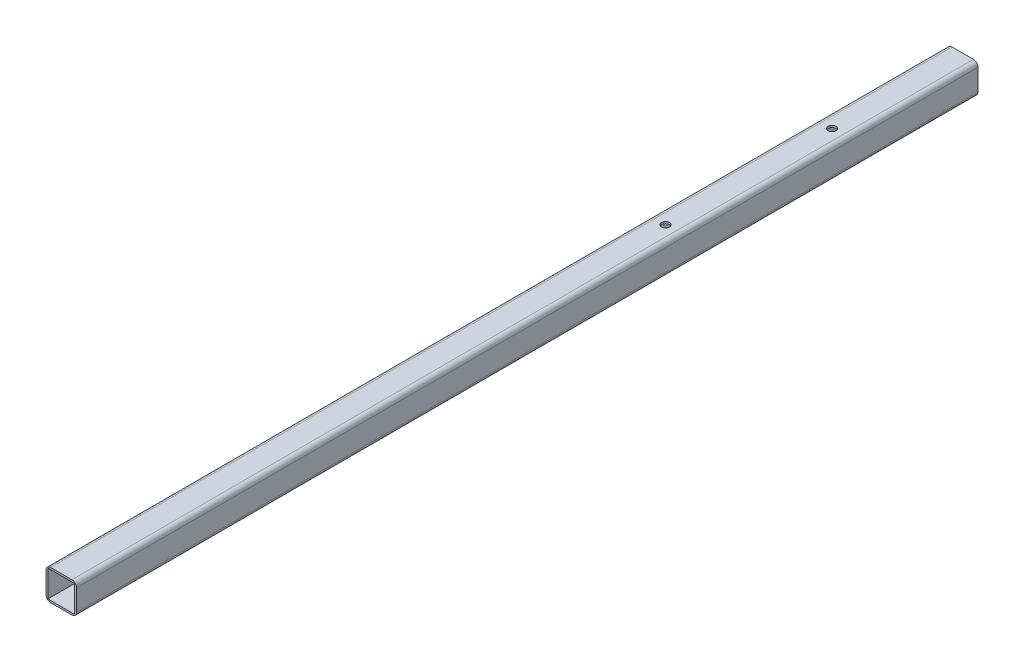
SolidWorks part; units mm, degrees
material "Alloy Steel"
ref_plane "Front Plane" through (0, 0, 0) normal (0, 0, 1) x (1, 0, 0)
ref_plane "Top Plane" through (0, 0, 0) normal (0, 1, 0) x (1, 0, 0)
ref_plane "Right Plane" through (0, 0, 0) normal (1, 0, 0) x (0, 0, -1)
sketch "Sketch4" plane through (0, 0, 0) normal (0, 0, 1) x (1, 0, 0)
  line L0 (-11.1125, 11.1125) -> (11.1125, 11.1125)
  line L1 (-12.7, -12.7) -> (12.7, -12.7)
  line L2 (-12.7, -12.7) -> (-12.7, 12.7)
  line L3 (-12.7, 12.7) -> (12.7, 12.7)
  line L4 (12.7, -12.7) -> (12.7, 12.7)
  line L5 (-12.7, -12.7) -> (12.7, 12.7) construction
  line L6 (-12.7, 12.7) -> (12.7, -12.7) construction
  line L7 (11.1125, -11.1125) -> (11.1125, 11.1125)
  line L8 (-11.1125, -11.1125) -> (11.1125, -11.1125)
  line L9 (-11.1125, -11.1125) -> (-11.1125, 11.1125)
  point P0 (0, 0)
  dimension "D1" = 25.4
  dimension "D2" = 25.4
  dimension "D3" = 1.5875
extrude "Boss-Extrude2" add sketch "Sketch4" along normal mid plane 749.3
fillet "Fillet1" radius 3.81 4 edges at (-12.7, -12.7, 0) (12.7, -12.7, 0) (-12.7, 12.7, 0) (12.7, 12.7, 0)
sketch "Sketch5" plane through (0, 12.7, 0) normal (0, 1, 0) x (1, 0, 0)
  circle A0 centre (0, 127.5955) radius 3.2639 construction
  circle A1 centre (0, 266.1045) radius 3.2639 construction
  circle A2 centre (0, 127.5955) radius 3.2639
  circle A3 centre (0, 266.1045) radius 3.2639
extrude "Cut-Extrude1" cut sketch "Sketch5" against normal through all both
